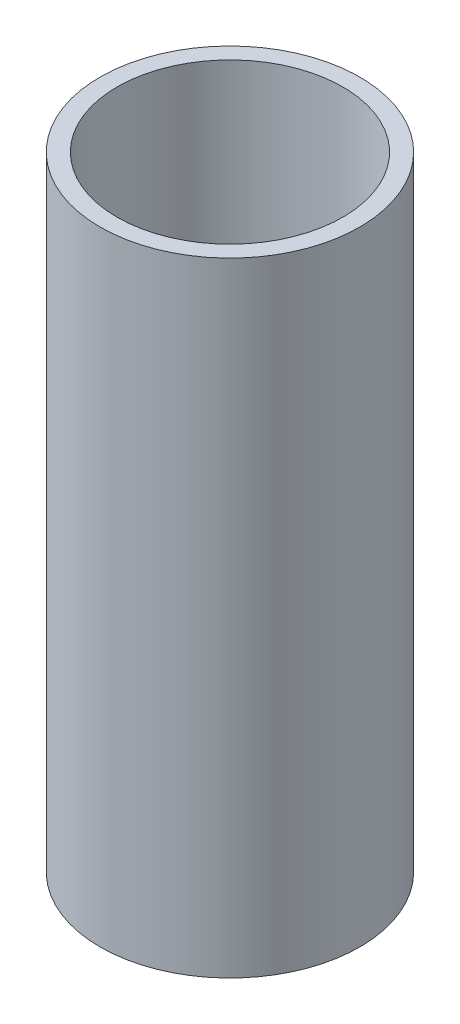
SolidWorks part; units mm, degrees
ref_plane "Front Plane" through (0, 0, 0) normal (0, 0, 1) x (1, 0, 0)
ref_plane "Top Plane" through (0, 0, 0) normal (0, 1, 0) x (1, 0, 0)
ref_plane "Right Plane" through (0, 0, 0) normal (1, 0, 0) x (0, 0, -1)
sketch "Sketch1" plane through (0, 0, 0) normal (0, 1, 0) x (1, 0, 0)
  circle A0 centre (0, 0) radius 28.575
  dimension "D1" = 57.15
extrude "Boss-Extrude1" add sketch "Sketch1" along normal blind 137.16
sketch "Sketch2" plane through (0, 137.16, 0) normal (0, 1, 0) x (1, 0, 0)
  circle A0 centre (0, 0) radius 24.8293
extrude "Cut-Extrude1" cut sketch "Sketch2" against normal blind 76.2
sketch "Sketch3" plane through (0, 0, 0) normal (0, -1, 0) x (1, 0, 0)
  circle A0 centre (0, 0) radius 20
  dimension "D1" = 40
extrude "Cut-Extrude2" cut sketch "Sketch3" against normal blind 20
